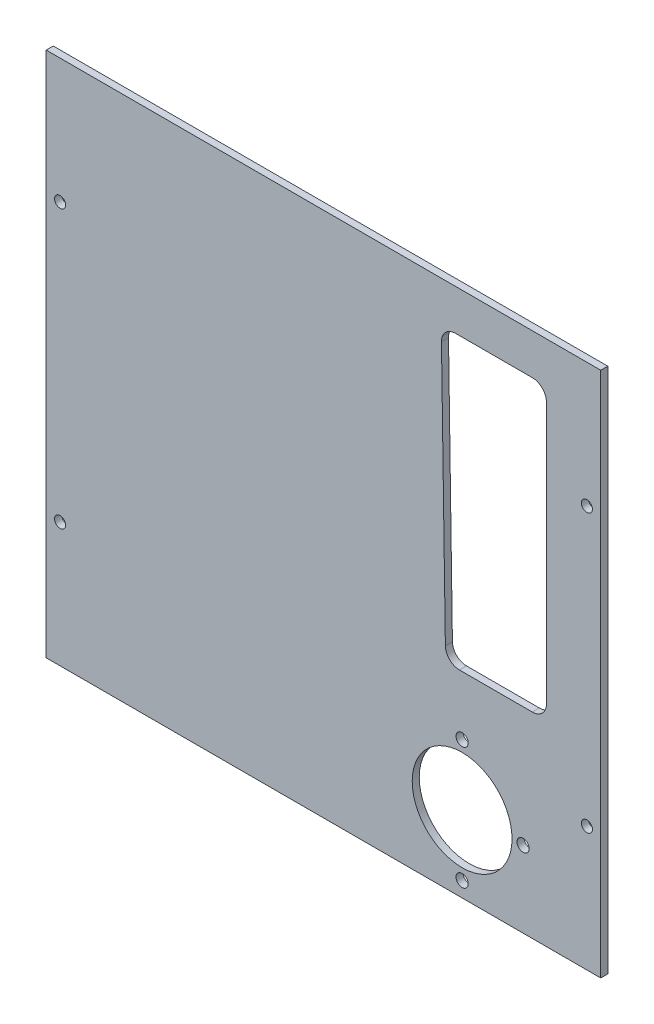
SolidWorks part; units mm, degrees
material "6061 Alloy"
ref_plane "Front Plane" through (0, 0, 0) normal (0, 0, 1) x (1, 0, 0)
ref_plane "Top Plane" through (0, 0, 0) normal (0, 1, 0) x (1, 0, 0)
ref_plane "Right Plane" through (0, 0, 0) normal (1, 0, 0) x (0, 0, -1)
sketch "Sketch1" plane through (0, 0, 0) normal (0, 0, 1) x (1, 0, 0)
  line L0 (0, 0) -> (0, 1.27)
  line L1 (0, 0) -> (100, 0)
  line L2 (0, 0) -> (0, 97.46)
  line L3 (0, 97.46) -> (100, 97.46)
  line L4 (100, 0) -> (100, 97.46)
  line L5 (0, 1.27) -> (100, 1.27)
  line L7 (0, 96.19) -> (0, 97.46)
  line L8 (0, 96.19) -> (100, 96.19)
  line L9 (100, 96.19) -> (100, 97.46)
  line L10 (100, 1.27) -> (100, 0)
extrude "Boss-Extrude1" add sketch "Sketch1" along normal blind 1.27
sketch "Sketch14" plane through (0, 0, 0) normal (0, 0, -1) x (-1, 0, 0)
  line L0 (-75, 0) -> (-75, 15) construction
  line L1 (-75, 0) -> (-75, 15) construction
  line L2 (-75, 0) -> (0, 0) construction
  line L3 (-67.8, 15) -> (-75, 15) construction
  line L4 (-70.5, 15) -> (-67, 15) construction
  line L5 (-67, 15) -> (-61, 15) construction
  line L6 (-100.0316, 0) -> (-49.9684, 0) construction
  line L7 (-49.9684, 0) -> (-75, 0) construction
  circle A3 centre (-75, 15) radius 9
  circle A4 centre (-75, 15) radius 8
  circle A5 centre (-75, 15) radius 14
  circle A6 centre (-64, 15) radius 1.1
  circle A7 centre (-75, 4) radius 1.1
  circle A8 centre (-86, 15) radius 1.1
  circle A9 centre (-75, 26) radius 1.1
  circle A10 centre (-75, 15) radius 6
  point P19 (-75, 15)
  point P22 (-75, 15)
  point P28 (-75, 15)
extrude "Cut-Extrude8" cut sketch "Sketch14" against normal blind 5 contours A10 | A4 A10 | A3 A4 | A9 | A8 | A7
sketch "Sketch15" plane through (0, 0, 0) normal (0, 0, -1) x (-1, 0, 0)
  line L0 (-2.5, 23.73) -> (-2.5, 73.73) construction
  line L1 (-50, 0) -> (-50, 97.46) construction
  line L2 (0, 48.73) -> (-2.5, 48.73) construction
  line L3 (0, 97.46) -> (0, 0) construction
  line L4 (-100, 97.46) -> (-100, 0) construction
  line L5 (-100, 48.73) -> (-97.5, 48.73) construction
  line L6 (-97.5, 23.73) -> (-97.5, 73.73) construction
  circle A4 centre (-2.5, 73.73) radius 1
  circle A5 centre (-2.5, 23.73) radius 1
  circle A6 centre (-97.5, 23.73) radius 1
  circle A7 centre (-97.5, 73.73) radius 1
extrude "Cut-Extrude9" cut sketch "Sketch15" against normal blind 10
sketch "Sketch18" plane through (0, 0, 1.27) normal (0, 0, 1) x (1, 0, 0)
  line L0 (87.6691, 88.8558) -> (73.8168, 88.8558)
  line L1 (71.2771, 86.2779) -> (71.9811, 39.1393)
  line L2 (74.5208, 36.6372) -> (87.6691, 36.6372)
  line L3 (90.2091, 39.1772) -> (90.2091, 86.3158)
  arc A0 (90.2091, 39.1772) -> (87.6691, 36.6372) centre (87.6691, 39.1772) cw
  arc A1 (74.5208, 36.6372) -> (71.9811, 39.1393) centre (74.5208, 39.1772) cw
  arc A2 (73.8168, 88.8558) -> (71.2771, 86.2779) centre (73.8168, 86.3158) ccw
  arc A3 (87.6691, 88.8558) -> (90.2091, 86.3158) centre (87.6691, 86.3158) cw
  dimension "D1" = 2.54
extrude "Cut-Extrude11" cut sketch "Sketch18" against normal blind 2.54
